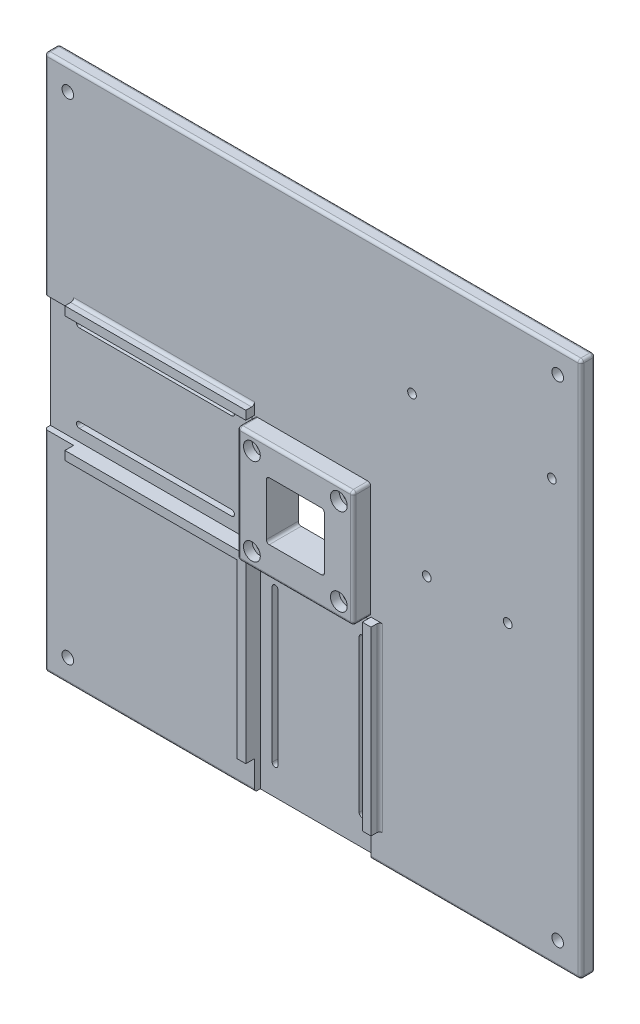
SolidWorks part; units mm, degrees
ref_plane "Plan de face" through (0, 0, 0) normal (0, 0, 1) x (1, 0, 0)
ref_plane "Plan de dessus" through (0, 0, 0) normal (0, 1, 0) x (1, 0, 0)
ref_plane "Plan de droite" through (0, 0, 0) normal (1, 0, 0) x (0, 0, -1)
sketch "Esquisse1" plane through (0, 0, 0) normal (0, 0, 1) x (1, 0, 0)
  line L1 (-92.5, 92.5) -> (92.5, 92.5)
  line L2 (-92.5, 92.5) -> (-92.5, -92.5)
  line L3 (-92.5, -92.5) -> (92.5, -92.5)
  line L4 (92.5, 92.5) -> (92.5, -92.5)
  dimension "D1" = 92.5
  dimension "D2" = 185
  dimension "D3" = 92.5
  dimension "D4" = 185
extrude "Boss.-Extru.1" add sketch "Esquisse1" along normal blind 5
fillet "Congé1" radius 1 12 edges at (0, -92.5, 5) (-92.5, 0, 5) (0, 92.5, 5) (92.5, 0, 5) (-92.5, -92.5, 2.5) (92.5, -92.5, 2.5) (-92.5, 92.5, 2.5) (92.5, 92.5, 2.5) (0, -92.5, 0) (-92.5, 0, 0) (0, 92.5, 0) (92.5, 0, 0)
sketch "Esquisse4" plane through (0, 0, 5) normal (0, 0, 1) x (1, 0, 0)
  line L1 (-10, 10) -> (10, 10)
  line L2 (-10, 10) -> (-10, -10)
  line L3 (-10, -10) -> (10, -10)
  line L4 (10, 10) -> (10, -10)
  circle A0 centre (-15, 15) radius 1.5
  circle A1 centre (15, 15) radius 1.5
  circle A2 centre (15, -15) radius 1.5
  circle A3 centre (-15, -15) radius 1.5
  point P4 (0, 0)
  dimension "D5" = 3
  dimension "D1" = 10
  dimension "D2" = 20
  dimension "D3" = 10
  dimension "D4" = 20
  dimension "D6" = 5
  dimension "D7" = 5
  dimension "D8" = 5
  dimension "D9" = 5
sketch "Esquisse9" plane through (0, 0, 0) normal (0, 0, -1) x (-1, 0, 0)
  line L0 (-92.5, -92.5) -> (-92.5, 92.5) construction
  line L1 (92.5, -92.5) -> (-92.5, -92.5) construction
  line L2 (-92.5, 92.5) -> (92.5, 92.5) construction
  line L3 (92.5, 92.5) -> (92.5, -92.5) construction
  circle A0 centre (-84.5, 84.5) radius 2
  circle A1 centre (84.5, 84.5) radius 2
  circle A2 centre (84.5, -84.5) radius 2
  circle A3 centre (-84.5, -84.5) radius 2
  dimension "D2" = 4
  dimension "D5" = 8
  dimension "D6" = 8
  dimension "D7" = 8
  dimension "D8" = 8
extrude "Enlèv. mat.-Extru.4" cut sketch "Esquisse9" against normal up to next
extrude "Enlèv. mat.-Extru.5" cut sketch "Esquisse4" against normal through all and the other way through all
sketch "Esquisse11" plane through (0, 0, 5) normal (0, 0, 1) x (1, 0, 0)
  line L0 (-10, -10) -> (10, -10) construction
  line L1 (-20, -20) -> (20, -20)
  line L2 (-20, -20) -> (-20, 20)
  line L3 (-20, 20) -> (20, 20)
  line L4 (20, -20) -> (20, 20)
  line L5 (-10, 10) -> (-10, -10) construction
  line L6 (10, 10) -> (-10, 10) construction
  line L7 (10, -10) -> (10, 10) construction
  dimension "D1" = 10
  dimension "D2" = 10
  dimension "D3" = 10
  dimension "D4" = 10
extrude "Boss.-Extru.3" add sketch "Esquisse11" along normal blind 6 contours L2 L3 L4 L1
fillet "Congé2" radius 1 12 edges at (10, -10, 2.5) (-10, -10, 2.5) (10, 10, 2.5) (-10, 10, 2.5) (-20, 0, 11) (0, 20, 11) (20, 0, 11) (0, -20, 11) (20, 20, 8) (20, -20, 8) (-20, -20, 8) (-20, 20, 8)
sketch "Esquisse12" plane through (0, 0, 11) normal (0, 0, 1) x (1, 0, 0)
  line L0 (-9, -10) -> (9, -10) construction
  line L1 (-9, -10) -> (9, -10)
  line L4 (19, 19) -> (-19, 19)
  line L5 (19, 19) -> (-19, 19)
  line L6 (-19, 19) -> (-19, -19)
  line L7 (-19, 19) -> (-19, -19)
  line L12 (10, -9) -> (10, 9)
  line L13 (-9, -10) -> (9, -10)
  line L14 (-10, 9) -> (-10, -9)
  line L15 (9, 10) -> (-9, 10)
  line L16 (10, -9) -> (10, 9)
  line L17 (-9, -10) -> (9, -10)
  line L18 (-10, 9) -> (-10, -9)
  line L19 (9, 10) -> (-9, 10)
  line L22 (-19, -19) -> (19, -19)
  line L23 (-19, -19) -> (19, -19)
  line L24 (19, -19) -> (19, 19)
  line L25 (19, -19) -> (19, 19)
  circle A0 centre (-15, -15) radius 1.5 construction
  circle A1 centre (15, -15) radius 1.5 construction
  circle A2 centre (15, 15) radius 1.5 construction
  circle A3 centre (-15, 15) radius 1.5 construction
  circle A4 centre (-15, -15) radius 1.5
  circle A5 centre (15, -15) radius 1.5
  circle A6 centre (15, 15) radius 1.5
  circle A7 centre (-15, 15) radius 1.5
  arc A12 (9, -10) -> (10, -9) centre (9, -9) ccw
  arc A13 (-10, -9) -> (-9, -10) centre (-9, -9) ccw
  arc A14 (-9, 10) -> (-10, 9) centre (-9, 9) ccw
  arc A15 (10, 9) -> (9, 10) centre (9, 9) ccw
  arc A16 (9, -10) -> (10, -9) centre (9, -9) ccw
  arc A17 (-10, -9) -> (-9, -10) centre (-9, -9) ccw
  arc A18 (-9, 10) -> (-10, 9) centre (-9, 9) ccw
  arc A19 (10, 9) -> (9, 10) centre (9, 9) ccw
  dimension "D1" = 0
  dimension "D2" = 0
extrude "Enlèv. mat.-Extru.6" cut sketch "Esquisse12" against normal through all contours L16 A19 L19 A18 L18 A17 L1 A16 | A6 | A7 | A5 | A4
sketch "Esquisse13" plane through (0, 0, 11) normal (0, 0, 1) x (1, 0, 0)
  circle A0 centre (-15, 15) radius 2.9
  circle A1 centre (15, 15) radius 2.9
  circle A2 centre (15, -15) radius 2.9
  circle A3 centre (-15, -15) radius 2.9
  dimension "D1" = 5.8
extrude "Enlèv. mat.-Extru.7" cut sketch "Esquisse13" against normal blind 3
sketch "Esquisse14" plane through (0, 0, 5) normal (0, 0, 1) x (1, 0, 0)
  line L0 (-82.5, 15) -> (-30, 15) construction
  line L1 (-82.5, 16) -> (-30, 16)
  line L2 (-82.5, 14) -> (-30, 14)
  line L3 (-92.5, -91.5) -> (-92.5, 91.5) construction
  line L4 (-20, -19) -> (-20, 19) construction
  line L5 (-30, -15) -> (-82.5, -15) construction
  line L6 (-30, -16) -> (-82.5, -16)
  line L7 (-30, -14) -> (-82.5, -14)
  line L8 (15, -30) -> (15, -82.5) construction
  line L9 (16, -30) -> (16, -82.5)
  line L10 (14, -30) -> (14, -82.5)
  line L11 (-15, -82.5) -> (-15, -30) construction
  line L12 (-16, -82.5) -> (-16, -30)
  line L13 (-14, -82.5) -> (-14, -30)
  line L14 (-19, -20) -> (19, -20) construction
  line L15 (91.5, -92.5) -> (-91.5, -92.5) construction
  arc A0 (-82.5, 16) -> (-82.5, 14) centre (-82.5, 15) ccw
  arc A1 (-30, 14) -> (-30, 16) centre (-30, 15) ccw
  arc A2 (-30, -16) -> (-30, -14) centre (-30, -15) ccw
  arc A3 (-82.5, -14) -> (-82.5, -16) centre (-82.5, -15) ccw
  arc A4 (16, -30) -> (14, -30) centre (15, -30) ccw
  arc A5 (14, -82.5) -> (16, -82.5) centre (15, -82.5) ccw
  arc A6 (-16, -82.5) -> (-14, -82.5) centre (-15, -82.5) ccw
  arc A7 (-14, -30) -> (-16, -30) centre (-15, -30) ccw
  point P2 (-56.25, 15)
  point P11 (-20, 0)
  point P14 (-56.25, -15)
  point P21 (15, -56.25)
  point P26 (-15, -56.25)
  point P33 (0, -20)
  dimension "D1" = 2
  dimension "D2" = 10
  dimension "D3" = 10
  dimension "D4" = 15
  dimension "D5" = 2
  dimension "D6" = 10
  dimension "D7" = 10
  dimension "D8" = 30
  dimension "D9" = 2
  dimension "D10" = 2
  dimension "D11" = 15
  dimension "D12" = 30
  dimension "D13" = 10
  dimension "D14" = 10
  dimension "D15" = 10
  dimension "D16" = 10
extrude "Enlèv. mat.-Extru.8" cut sketch "Esquisse14" against normal through all
sketch "Esquisse15" plane through (0, 0, 5) normal (0, 0, 1) x (1, 0, 0)
  line L0 (-20.1, -20.1) -> (-20.1, -82.5)
  line L1 (-20.1, 20.1) -> (-82.5, 20.1)
  line L2 (-20.1, 20.1) -> (-20.1, 23.1)
  line L3 (-20.1, 23.1) -> (-82.5, 23.1)
  line L4 (-82.5, 20.1) -> (-82.5, 23.1)
  line L5 (-20.1, -20.1) -> (-82.5, -20.1)
  line L7 (-23.1, -23.1) -> (-82.5, -23.1)
  line L8 (-82.5, -20.1) -> (-82.5, -23.1)
  line L9 (-20.1, -82.5) -> (-23.1, -82.5)
  line L10 (-23.1, -82.5) -> (-23.1, -23.1)
  line L12 (23.1, -20.1) -> (20.1, -20.1)
  line L13 (23.1, -20.1) -> (23.1, -82.5)
  line L14 (23.1, -82.5) -> (20.1, -82.5)
  line L15 (20.1, -20.1) -> (20.1, -82.5)
  dimension "D1" = 3
  dimension "D2" = 3
  dimension "D3" = 3
  dimension "D4" = 3
  dimension "D5" = 20.1
  dimension "D6" = 40.2
  dimension "D7" = 20.1
  dimension "D8" = 40.2
extrude "Boss.-Extru.4" add sketch "Esquisse15" along normal blind 3
fillet "Congé3" radius 1 4 edges at (-51.3, 23.1, 5) (-52.8, -23.1, 5) (-23.1, -52.8, 5) (23.1, -51.3, 5)
sketch "Esquisse20" plane through (0, 0, 5) normal (0, 0, 1) x (1, 0, 0)
  line L0 (-91.5, 92.5) -> (91.5, 92.5) construction
  line L1 (92.5, 91.5) -> (92.5, -91.5) construction
  circle A1 centre (39.32, 1.7) radius 1.5
  circle A5 centre (34.24, 53.77) radius 1.5
  circle A6 centre (82.5, 52.5) radius 1.5
  circle A7 centre (67.26, 1.7) radius 1.5
  dimension "D1" = 3
  dimension "D2" = 3
  dimension "D3" = 3
  dimension "D4" = 3
  dimension "D6" = 48.26
  dimension "D8" = 15.24
  dimension "D9" = 1.27
  dimension "D10" = 40
  dimension "D11" = 10
  dimension "D5" = 27.94
  dimension "D7" = 50.8
extrude "Enlèv. mat.-Extru.12" cut sketch "Esquisse20" against normal blind 10
sketch "Esquisse21" plane through (0, 0, 5) normal (0, 0, 1) x (1, 0, 0)
  line L1 (-95.7156, 20.1) -> (-21, 20.1)
  line L2 (-95.7156, 20.1) -> (-95.7156, -20.1)
  line L3 (-95.7156, -20.1) -> (-21, -20.1)
  line L9 (-82.5, 20.1) -> (-20.1, 20.1) construction
  line L10 (-20.1, -20.1) -> (-82.5, -20.1) construction
  line L11 (-21, 20.1) -> (-21, -20.1)
  line L12 (-20, -19) -> (-20, 19) construction
  dimension "D1" = 1
extrude "Enlèv. mat.-Extru.13" cut sketch "Esquisse21" against normal blind 2
sketch "Esquisse22" plane through (0, 0, 5) normal (0, 0, 1) x (1, 0, 0)
  line L5 (-20.1, -82.5) -> (-20.1, -20.1) construction
  line L7 (20.1, -21.1) -> (20.1, -100.2038)
  line L8 (20.1, -100.2038) -> (-20.1, -100.2038)
  line L9 (-20.1, -21.1) -> (-20.1, -100.2038)
  line L10 (20.1, -20.1) -> (20.1, -82.5) construction
  line L11 (-20.1, -21.1) -> (20.1, -21.1)
  dimension "D1" = 1
extrude "Enlèv. mat.-Extru.20" cut sketch "Esquisse22" against normal blind 2
